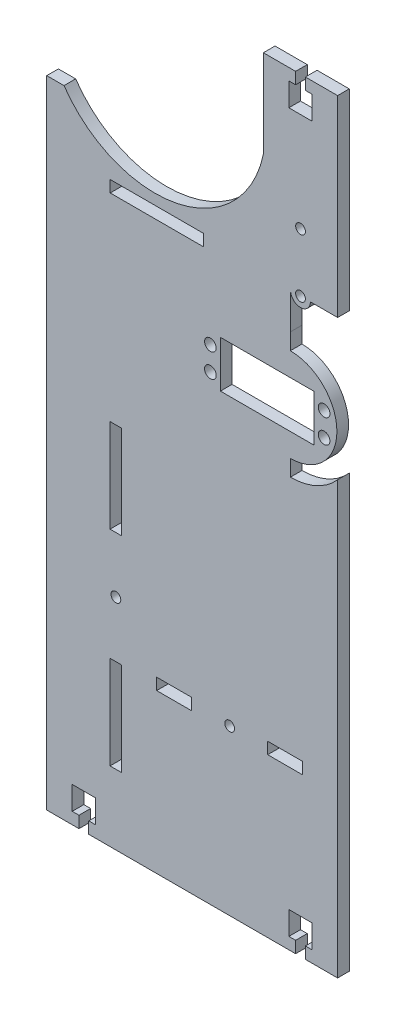
SolidWorks part; units mm, degrees
ref_plane "Front Plane" through (0, 0, 0) normal (0, 0, 1) x (1, 0, 0)
ref_plane "Top Plane" through (0, 0, 0) normal (0, 1, 0) x (1, 0, 0)
ref_plane "Right Plane" through (0, 0, 0) normal (1, 0, 0) x (0, 0, -1)
sketch "Sketch1" plane through (0, 0, 0) normal (0, 0, 1) x (1, 0, 0)
  line L1 (15.93, -164) -> (-15.93, -164)
  line L2 (15.93, -164) -> (15.93, 164)
  line L3 (15.93, 164) -> (-15.93, 164)
  line L4 (-15.93, -164) -> (-15.93, 164)
  line L5 (15.93, -164) -> (-15.93, 164) construction
  line L6 (15.93, 164) -> (-15.93, -164) construction
  point P0 (0, 0)
  dimension "D1" = 328
  dimension "D2" = 31.86
extrude "Boss-Extrude1" add sketch "Sketch1" along normal blind 5
sketch "Sketch2" plane through (0, 0, 5) normal (0, 0, 1) x (1, 0, 0)
  line L3 (15.93, 81.5) -> (-15.93, 81.5) construction
  line L4 (15.93, -164) -> (15.93, 164) construction
  line L5 (-15.93, 164) -> (-15.93, -164) construction
  circle A0 centre (0, 81.5) radius 2.1
  dimension "D1" = 4.2
extrude "Cut-Extrude1" cut sketch "Sketch2" against normal blind 10
sketch "Sketch3" plane through (0, 0, 5) normal (0, 0, 1) x (1, 0, 0)
  line L0 (0, 164) -> (0, -164) construction
  line L1 (15.93, 164) -> (-15.93, 164) construction
  line L2 (-15.93, -164) -> (15.93, -164) construction
  line L3 (2.1, 164) -> (2.1, 159)
  line L4 (2.1, 159) -> (5, 159)
  line L5 (2.1, 164) -> (-2.1, 164)
  line L6 (5, 159) -> (5, 149)
  line L7 (5, 149) -> (-5, 149)
  line L8 (-5, 159) -> (-5, 149)
  line L9 (-2.1, 159) -> (-5, 159)
  line L10 (-2.1, 164) -> (-2.1, 159)
  line L11 (15.93, 0) -> (-6.7077, 0) construction
  line L12 (15.93, -164) -> (15.93, 164) construction
  line L13 (-2.1, -164) -> (-2.1, -159)
  line L14 (-2.1, -159) -> (-5, -159)
  line L15 (-5, -159) -> (-5, -149)
  line L16 (5, -149) -> (-5, -149)
  line L17 (5, -159) -> (5, -149)
  line L18 (2.1, -164) -> (-2.1, -164)
  line L19 (2.1, -159) -> (5, -159)
  line L20 (2.1, -164) -> (2.1, -159)
  point P12 (0, 149)
  point P28 (0, -149)
  dimension "D1" = 2.1
  dimension "D2" = 5
  dimension "D3" = 5
  dimension "D4" = 10
extrude "Cut-Extrude2" cut sketch "Sketch3" against normal blind 10
sketch "Sketch4" plane through (0, 0, 0) normal (0, 0, -1) x (-1, 0, 0)
  line L2 (108.9134, -164) -> (15.93, -164)
  line L3 (108.9134, -164) -> (108.9134, 164) construction
  line L6 (20.9306, 109) -> (15.9468, 109) construction
  line L7 (108.9134, 109) -> (101.5035, 109)
  line L8 (108.9002, 109) -> (103.9163, 109) construction
  line L9 (108.9134, -164) -> (108.9134, 109)
  line L13 (15.93, 164) -> (15.93, -164) construction
  line L14 (15.93, 109) -> (15.93, -164)
  line L15 (15.93, 109) -> (15.93, 126.2733)
  arc A0 (23.3434, 109) -> (101.5035, 109) centre (62.4234, 136) ccw
  arc A1 (15.93, 126.2733) -> (101.5035, 109) centre (62.4234, 136) ccw
  line M17 (15.93, -164) -> (15.93, 164)
  dimension "D1" = 95
extrude "Boss-Extrude2" add sketch "Sketch4" against normal blind 5 contours A1 L2 L9 L7 A0 M17
sketch "Sketch7" plane through (0, 0, 5) normal (0, 0, 1) x (1, 0, 0)
  line L0 (-2.0785, 109) -> (-2.0785, 104) construction
  line L2 (2.1215, 109) -> (2.1215, 104) construction
  line L3 (-2.0785, 109) -> (-2.0785, 104) construction
  line L4 (2.1215, 109) -> (2.1215, 104) construction
  line L5 (2.1215, 106.5) -> (-2.0785, 106.5) construction
  line L6 (-92.9834, -164) -> (-92.9834, -151.8602) construction
  line L7 (-108.9134, -164) -> (-2.1, -164) construction
  line L8 (-108.9134, -164) -> (-108.9134, 109) construction
  line L10 (-90.8834, -164) -> (-95.0834, -164)
  line L11 (-90.8834, -164) -> (-90.8834, -159)
  line L12 (-90.8834, -159) -> (-95.0834, -159)
  line L13 (-95.0834, -164) -> (-95.0834, -159)
  line L14 (-87.9834, -149) -> (-97.9834, -149)
  line L15 (-87.9834, -149) -> (-87.9834, -159)
  line L16 (-87.9834, -159) -> (-97.9834, -159)
  line L17 (-97.9834, -149) -> (-97.9834, -159)
  circle A0 centre (0.0215, 106.5) radius 2.1
  point P22 (-92.9834, -164)
  point P23 (-92.9834, -149)
  line M21 (-108.9134, -164) -> (-2.1, -164)
  dimension "D1" = 15.93
  dimension "D2" = 5
  dimension "D3" = 10
  dimension "D4" = 4.2
  dimension "D5" = 10
extrude "Cut-Extrude3" cut sketch "Sketch7" against normal blind 5 contours L14 L17 L16 L12 L15 | L13 L11 L12 M21 | A0
sketch "Sketch8" plane through (0, 0, 5) normal (0, 0, 1) x (1, 0, 0)
  line L0 (-33.1791, 49) -> (-40.2291, 49) construction
  line L1 (-34.37, 49) -> (5.8304, 49)
  line L2 (-34.37, 49) -> (-34.37, 29)
  line L3 (-34.37, 29) -> (5.8304, 29)
  line L4 (5.8304, 49) -> (5.8304, 29)
  line L5 (-34.37, 49) -> (5.8304, 29) construction
  line L6 (-34.37, 29) -> (5.8304, 49) construction
  line L7 (4.8209, 29) -> (11.8709, 29) construction
  circle A3 centre (-38.6791, 44.08) radius 2.5
  circle A4 centre (-38.6791, 33.92) radius 2.5
  circle A5 centre (10.13, 44.08) radius 2.5
  circle A6 centre (10.13, 33.92) radius 2.5
  point P4 (-14.2698, 39)
extrude "Cut-Extrude4" cut sketch "Sketch8" against normal blind 10
sketch "Sketch9" plane through (0, 0, 0) normal (0, 0, -1) x (-1, 0, 0)
  line L0 (4.37, 12) -> (4.37, 19)
  line L1 (4.37, 59) -> (4.37, 66)
  arc A0 (4.37, 66) -> (4.37, 12) centre (4.37, 39) ccw
  arc A2 (4.37, 59) -> (4.37, 19) centre (4.37, 39) ccw
  point P9 (4.37, 39)
  dimension "D1" = 27
  dimension "D2" = 20
extrude "Cut-Extrude5" cut sketch "Sketch9" against normal blind 10
sketch "Sketch10" plane through (0, 0, 0) normal (0, 0, -1) x (-1, 0, 0)
  line L1 (-15.93, 56.802) -> (-15.93, 164) construction
  line L2 (-15.93, 66) -> (-15.93, 56.802)
  line L3 (4.25, 81.5) -> (4.37, 66)
  line L4 (-4.25, 81.5) -> (-15.93, 81.5)
  line L5 (-15.93, 81.5) -> (-15.93, 66)
  arc A0 (4.37, 66) -> (-15.93, 56.802) centre (4.37, 39) ccw construction
  arc A1 (4.37, 66) -> (-15.93, 56.802) centre (4.37, 39) ccw
  arc A2 (-4.25, 81.5) -> (4.25, 81.5) centre (0, 81.5) ccw
  dimension "D1" = 8.5
extrude "Cut-Extrude6" cut sketch "Sketch10" against normal blind 10
sketch "Sketch12" plane through (0, 0, 0) normal (0, 0, -1) x (-1, 0, 0)
  line L1 (61.7364, -96) -> (46.7364, -96)
  line L2 (61.7364, -96) -> (61.7364, -91)
  line L3 (61.7364, -91) -> (46.7364, -91)
  line L4 (46.7364, -96) -> (46.7364, -91)
  line L5 (14.07, -96) -> (-0.93, -96)
  line L6 (14.07, -96) -> (14.07, -91)
  line L7 (14.07, -91) -> (-0.93, -91)
  line L8 (-0.93, -96) -> (-0.93, -91)
  line L9 (46.7364, -93.5) -> (14.07, -93.5) construction
  line L10 (90.8834, -164) -> (2.1, -164) construction
  line L11 (76.7364, -134) -> (81.7364, -134)
  line L12 (76.7364, -134) -> (76.7364, -94)
  line L13 (76.7364, -94) -> (81.7364, -94)
  line L14 (81.7364, -134) -> (81.7364, -94)
  line L15 (43.6203, 24) -> (71.1363, 24) construction
  line L16 (76.7364, -46) -> (81.7364, -46)
  line L17 (76.7364, -46) -> (76.7364, -6)
  line L18 (76.7364, -6) -> (81.7364, -6)
  line L19 (81.7364, -46) -> (81.7364, -6)
  line L20 (79.2364, -94) -> (79.2364, -46) construction
  circle A0 centre (30.4032, -93.5) radius 2.1
  circle A1 centre (79.2364, -70) radius 2.1
  dimension "D9" = 4.2
  dimension "D1" = 15
  dimension "D2" = 40
  dimension "D3" = 30
  dimension "D4" = 5
  dimension "D5" = 5
  dimension "D6" = 40
  dimension "D7" = 15
  dimension "D8" = 30
extrude "Cut-Extrude7" cut sketch "Sketch12" against normal blind 5
sketch "Sketch15" plane through (0, 0, 5) normal (0, 0, 1) x (1, 0, 0)
  line L1 (-41.675, 79) -> (-81.675, 79)
  line L2 (-41.675, 79) -> (-41.675, 84)
  line L3 (-41.675, 84) -> (-81.675, 84)
  line L4 (-81.675, 79) -> (-81.675, 84)
  line L6 (-81.675, 79) -> (-81.675, 84) construction
  line L7 (-108.1679, 79) -> (-81.675, 79) construction
  dimension "D1" = 40
  dimension "D2" = 5
  dimension "D3" = 0
  dimension "D4" = 0
extrude "Cut-Extrude8" cut sketch "Sketch15" against normal blind 5
